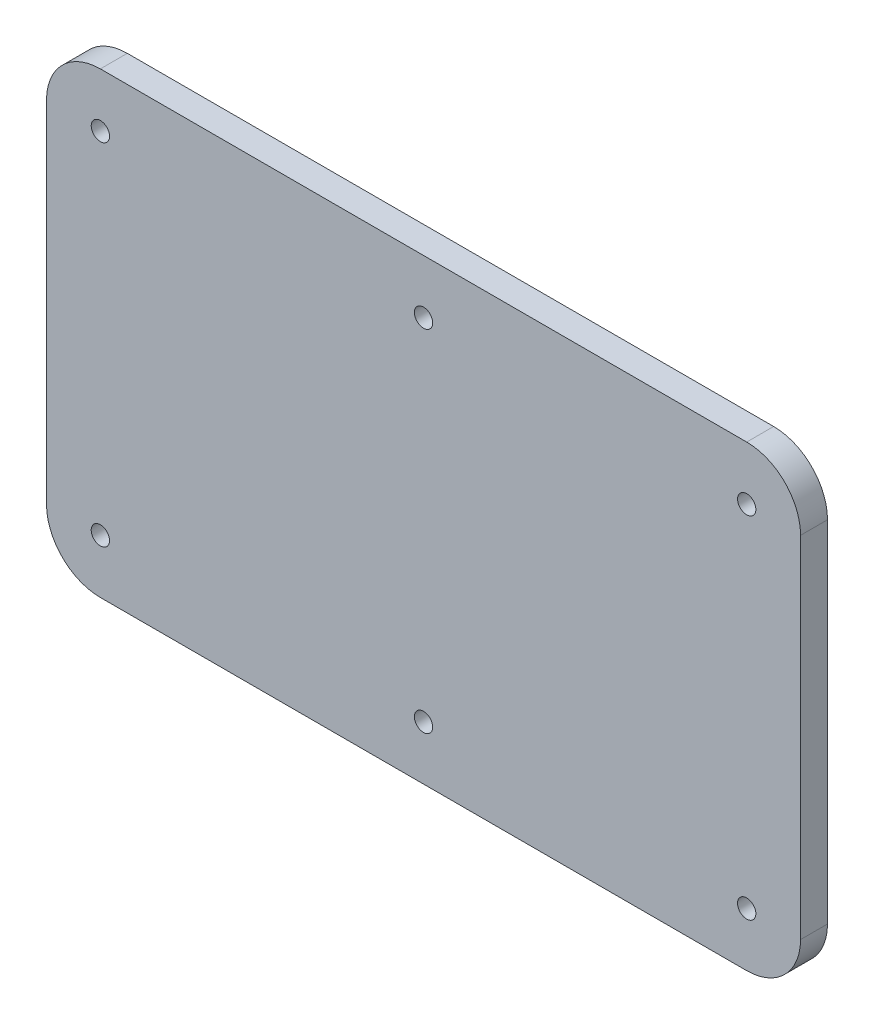
SolidWorks part; units mm, degrees
ref_plane "Front Plane" through (0, 0, 0) normal (0, 0, 1) x (1, 0, 0)
ref_plane "Top Plane" through (0, 0, 0) normal (0, 1, 0) x (1, 0, 0)
ref_plane "Right Plane" through (0, 0, 0) normal (1, 0, 0) x (0, 0, -1)
sketch "Sketch1" plane through (0, 0, 0) normal (0, 0, 1) x (1, 0, 0)
  line L0 (0, 0) -> (0, 32.5) construction
  line L1 (-60, -42.5) -> (60, -42.5)
  line L2 (-70, -32.5) -> (-70, 32.5)
  line L3 (-60, 42.5) -> (60, 42.5)
  line L4 (70, -32.5) -> (70, 32.5)
  line L5 (-70, -42.5) -> (70, 42.5) construction
  line L6 (-70, 42.5) -> (70, -42.5) construction
  arc A0 (-60, 42.5) -> (-70, 32.5) centre (-60, 32.5) ccw
  arc A1 (-60, -42.5) -> (-70, -32.5) centre (-60, -32.5) cw
  arc A2 (70, -32.5) -> (60, -42.5) centre (60, -32.5) cw
  arc A3 (70, 32.5) -> (60, 42.5) centre (60, 32.5) ccw
  circle A4 centre (-60, 32.5) radius 1.7
  circle A5 centre (-60, -32.5) radius 1.7
  circle A6 centre (60, -32.5) radius 1.7
  circle A7 centre (60, 32.5) radius 1.7
  circle A8 centre (0, 32.5) radius 1.7
  circle A9 centre (0, -32.5) radius 1.7
  point P0 (0, 0)
  dimension "D3" = 10
  dimension "D4" = 10
  dimension "D5" = 10
  dimension "D6" = 10
  dimension "D1" = 140
  dimension "D2" = 85
extrude "Boss-Extrude1" add sketch "Sketch1" along normal blind 5
